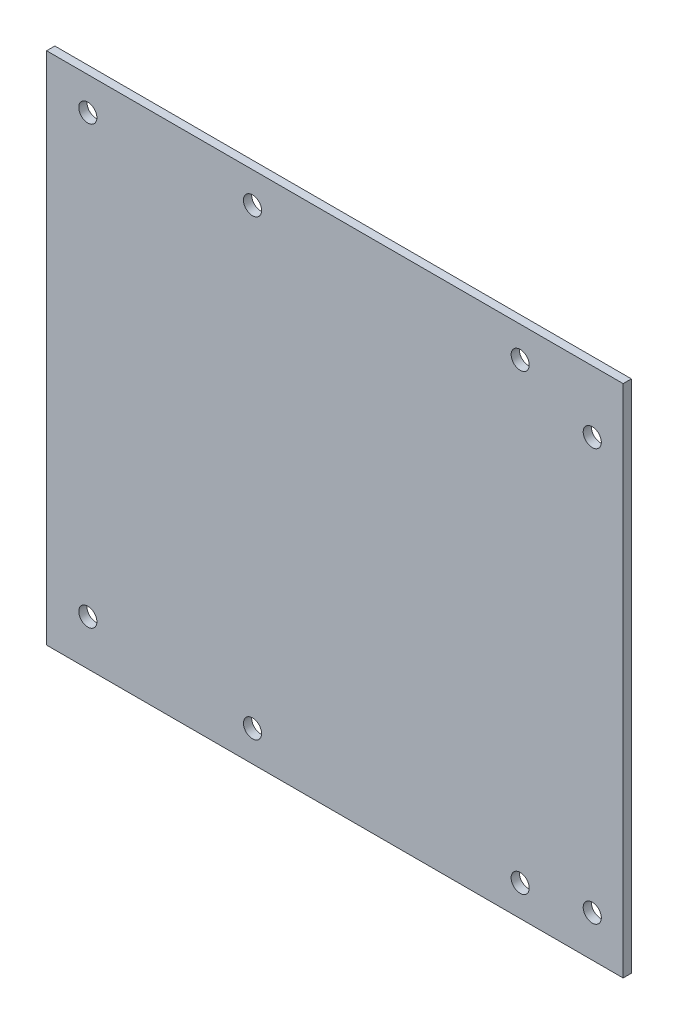
SolidWorks part; units mm, degrees
ref_plane "正面" through (0, 0, 0) normal (0, 0, 1) x (1, 0, 0)
ref_plane "平面" through (0, 0, 0) normal (0, 1, 0) x (1, 0, 0)
ref_plane "右側面" through (0, 0, 0) normal (1, 0, 0) x (0, 0, -1)
sketch "ｽｹｯﾁ1" plane through (0, 0, 0) normal (0, 0, 1) x (1, 0, 0)
  line L1 (-70, 62.5) -> (70, 62.5)
  line L2 (-70, 62.5) -> (-70, -62.5)
  line L3 (-70, -62.5) -> (70, -62.5)
  line L4 (70, 62.5) -> (70, -62.5)
  line L5 (-70, 62.5) -> (70, -62.5) construction
  line L6 (-70, -62.5) -> (70, 62.5) construction
  point P0 (0, 0)
  dimension "D1" = 125
  dimension "D2" = 140
extrude "ﾎﾞｽ - 押し出し1" add sketch "ｽｹｯﾁ1" along normal blind 2
sketch "ｽｹｯﾁ3" plane through (0, 0, 2) normal (0, 0, 1) x (1, 0, 0)
  line L0 (-70, 62.5) -> (-60, 62.5)
  line L1 (70, 62.5) -> (-70, 62.5) construction
  line L2 (-60, 62.5) -> (-60, 54.5)
  line L3 (-60, 54.5) -> (-60, -51.5)
  circle A0 centre (-60, 54.5) radius 2.2
  circle A1 centre (-60, -51.5) radius 2.2
  dimension "D4" = 4.4
  dimension "D5" = 4.4
  dimension "D1" = 10
  dimension "D2" = 8
  dimension "D3" = 106
extrude "ｶｯﾄ - 押し出し1" cut sketch "ｽｹｯﾁ3" against normal blind 2
sketch "ｽｹｯﾁ6" plane through (0, 0, 2) normal (0, 0, 1) x (1, 0, 0)
  line L0 (70, -62.5) -> (62.5, -62.5)
  line L1 (-70, -62.5) -> (70, -62.5) construction
  line L2 (62.5, -62.5) -> (62.5, -52.5)
  line L3 (62.5, -52.5) -> (62.5, 47.5)
  circle A0 centre (62.5, -52.5) radius 2.2
  circle A1 centre (62.5, 47.5) radius 2.2
  dimension "D3" = 4.4
  dimension "D5" = 4.4
  dimension "D1" = 7.5
  dimension "D2" = 10
  dimension "D4" = 100
extrude "ｶｯﾄ - 押し出し2" cut sketch "ｽｹｯﾁ6" against normal blind 2
sketch "ｽｹｯﾁ7" plane through (0, 0, 2) normal (0, 0, 1) x (1, 0, 0)
  line L0 (70, 62.5) -> (70, 55)
  line L1 (70, -62.5) -> (70, 62.5) construction
  line L2 (70, 55) -> (45, 55)
  line L3 (45, 55) -> (-20, 55)
  line L4 (70, -62.5) -> (70, -55)
  line L5 (70, -55) -> (45, -55)
  line L6 (45, -55) -> (-20, -55)
  circle A0 centre (45, 55) radius 2.2
  circle A1 centre (-20, 55) radius 2.2
  circle A2 centre (45, -55) radius 2.2
  circle A3 centre (-20, -55) radius 2.2
  dimension "D3" = 4.4
  dimension "D5" = 4.4
  dimension "D9" = 4.4
  dimension "D10" = 4.4
  dimension "D1" = 7.5
  dimension "D2" = 25
  dimension "D4" = 65
  dimension "D6" = 7.5
  dimension "D7" = 25
  dimension "D8" = 65
extrude "ｶｯﾄ - 押し出し3" cut sketch "ｽｹｯﾁ7" against normal blind 105 contours L2 A0 L3 | L3 A0 L2 | A1 | A3 | A2
